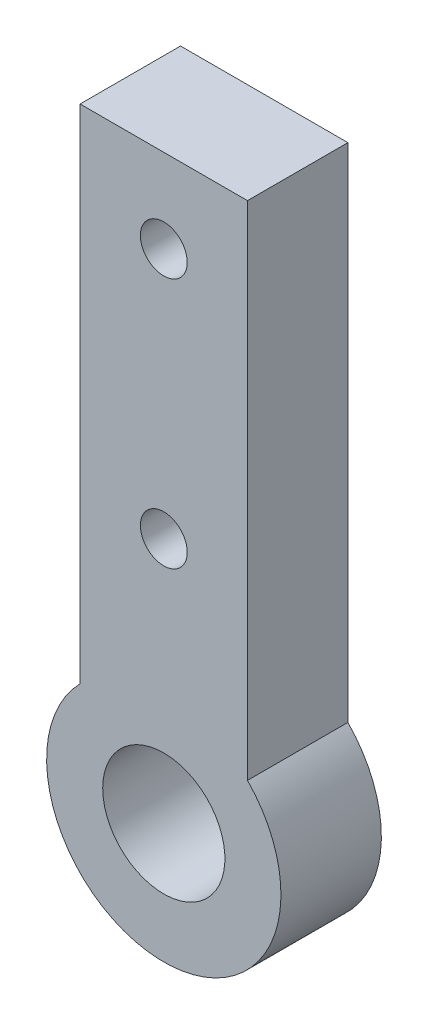
SolidWorks part; units mm, degrees
ref_plane "Plan de face" through (0, 0, 0) normal (0, 0, 1) x (1, 0, 0)
ref_plane "Plan de dessus" through (0, 0, 0) normal (0, 1, 0) x (1, 0, 0)
ref_plane "Plan de droite" through (0, 0, 0) normal (1, 0, 0) x (0, 0, -1)
sketch "Esquisse1" plane through (0, 0, 0) normal (0, 0, 1) x (1, 0, 0)
  line L1 (-5, 18.9279) -> (5, 18.9279)
  line L2 (-5, 18.9279) -> (-5, -11.0721)
  line L4 (5, 18.9279) -> (5, -11.0721)
  arc A0 (5, -11.0721) -> (-5, -11.0721) centre (0, -15.9711) cw
  dimension "D1" = 30
  dimension "D3" = 7
  dimension "D2" = 10
  dimension "D4" = 30
extrude "Boss.-Extru.1" add sketch "Esquisse1" along normal blind 6
sketch "Esquisse2" plane through (0, 0, 0) normal (0, 0, -1) x (-1, 0, 0)
  line L0 (-5, 18.9279) -> (5, 18.9279) construction
  circle A0 centre (0, -15.7996) radius 3.65
  circle A1 centre (0, -1.0721) radius 1.4
  circle A2 centre (0, 13.9279) radius 1.4
  dimension "D1" = 7.3
  dimension "D2" = 2.8
  dimension "D3" = 2.8
  dimension "D4" = 5
  dimension "D5" = 15
extrude "Enlèv. mat.-Extru.1" cut sketch "Esquisse2" against normal blind 6
